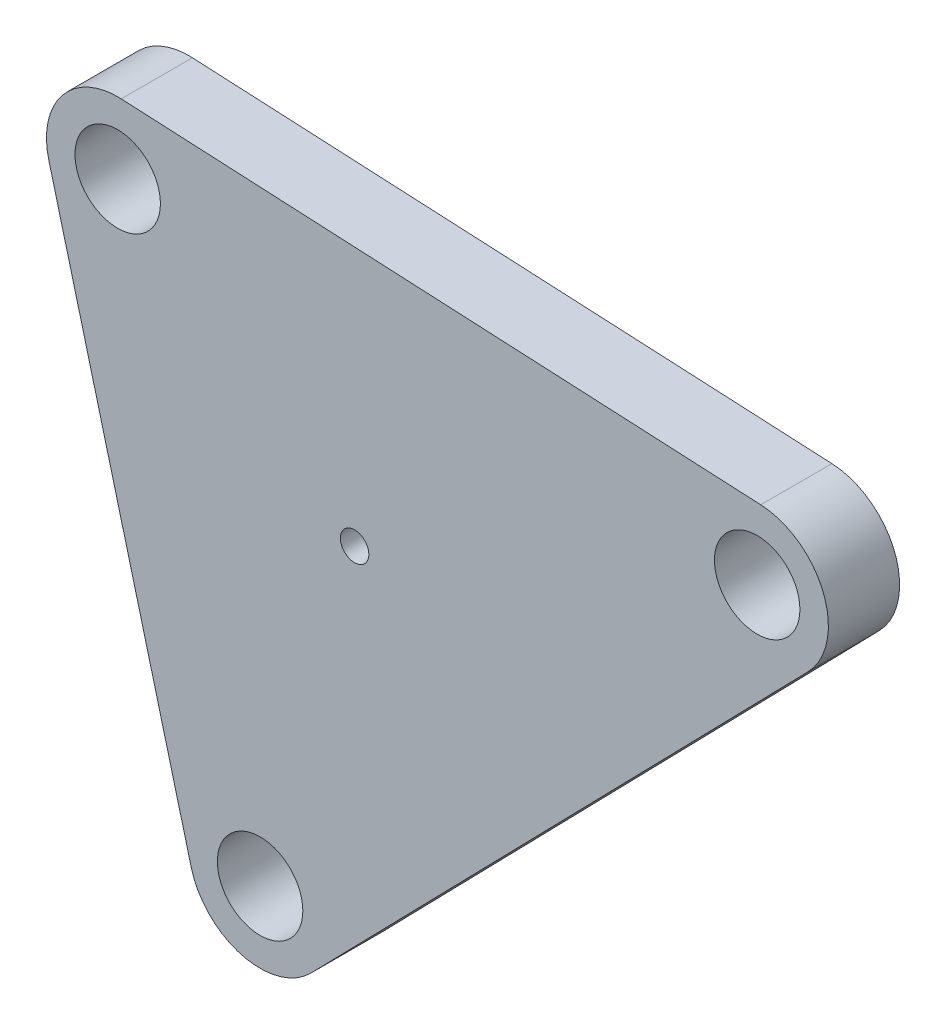
SolidWorks part; units mm, degrees
ref_plane "Plan de face" through (0, 0, 0) normal (0, 0, 1) x (1, 0, 0)
ref_plane "Plan de dessus" through (0, 0, 0) normal (0, 1, 0) x (1, 0, 0)
ref_plane "Plan de droite" through (0, 0, 0) normal (1, 0, 0) x (0, 0, -1)
sketch "Esquisse1" plane through (0, 0, 0) normal (0, 0, 1) x (1, 0, 0)
  line L0 (24.025, -4.1787) -> (24.4084, -35.2891) construction
  line L2 (24.025, -4.1787) -> (39.7718, -19.5422) construction
  line L4 (52.7306, -2.9523) -> (7.8301, -0.7237)
  line L5 (24.025, -4.1787) -> (8.6615, -19.9256) construction
  line L6 (39.7718, -19.5422) -> (24.4084, -35.2891) construction
  line L7 (8.6615, -19.9256) -> (24.4084, -35.2891) construction
  line L8 (2.7468, -6.99) -> (12.7468, -44.99)
  line L12 (21.1611, -47.2092) -> (56.0616, -11.4378)
  circle A0 centre (7.5822, -5.7175) radius 3
  circle A1 centre (52.4827, -7.9461) radius 3
  circle A2 centre (17.5822, -43.7175) radius 3
  arc A3 (7.8301, -0.7237) -> (2.7468, -6.99) centre (7.5822, -5.7175) ccw
  arc A4 (56.0616, -11.4378) -> (52.7306, -2.9523) centre (52.4827, -7.9461) ccw
  arc A5 (12.7468, -44.99) -> (21.1611, -47.2092) centre (17.5822, -43.7175) ccw
  circle A6 centre (24.2167, -19.7339) radius 1
extrude "Extrusion1" add sketch "Esquisse1" along normal blind 5
